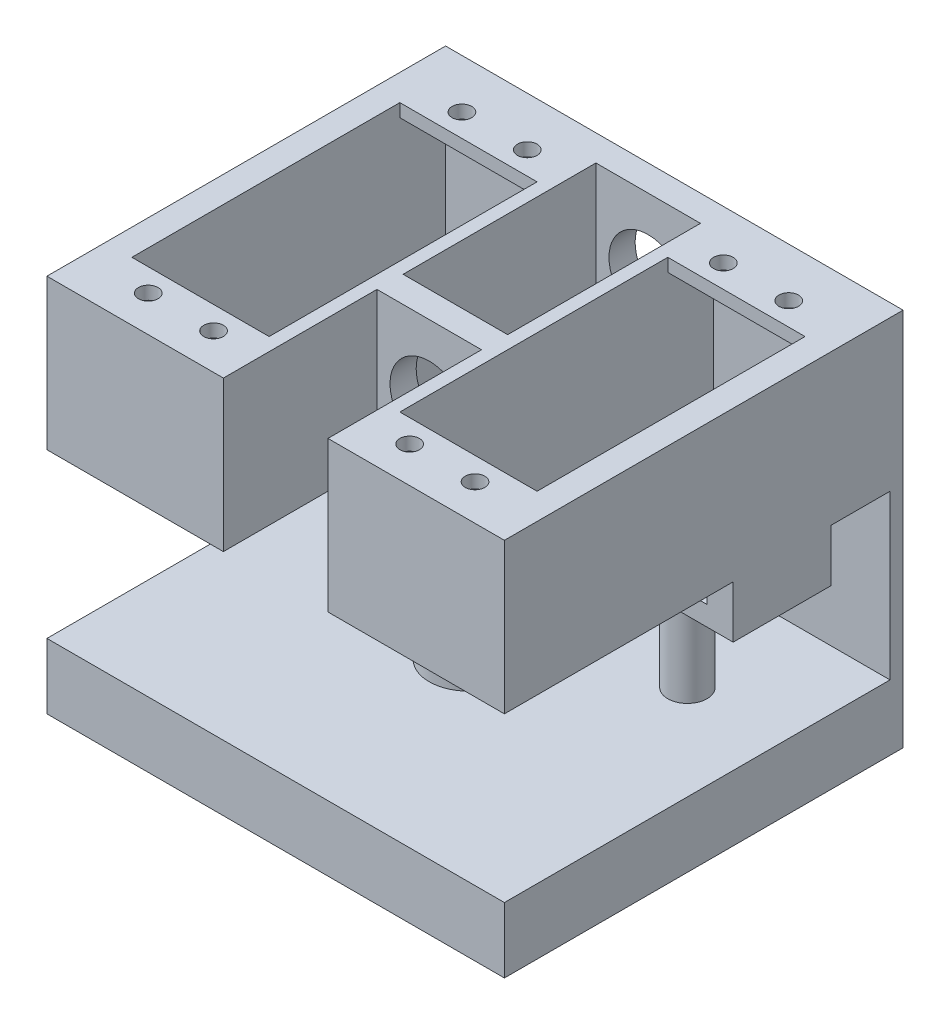
SolidWorks part; units mm, degrees
ref_plane "정면" through (0, 0, 0) normal (0, 0, 1) x (1, 0, 0)
ref_plane "윗면" through (0, 0, 0) normal (0, 1, 0) x (1, 0, 0)
ref_plane "우측면" through (0, 0, 0) normal (1, 0, 0) x (0, 0, -1)
sketch "스케치1" plane through (0, 0, 0) normal (0, 1, 0) x (1, 0, 0)
  line L0 (0, 0) -> (0, 59)
  line L1 (0, 59) -> (-25, 59)
  line L2 (-25, 59) -> (-25, 57)
  line L3 (0, 0) -> (-25, 0)
  line L4 (-45, 0) -> (-45, 2)
  line L5 (-66, 57) -> (-66, 2)
  line L6 (-45, 2) -> (-66, 2)
  line L7 (-45, 59) -> (-70, 59)
  line L8 (-70, 59) -> (-70, 0)
  line L9 (-70, 0) -> (-45, 0)
  line L10 (0, 0) -> (-4, 0)
  line L11 (-4, 2) -> (-4, 57)
  line L12 (-4, 57) -> (-25, 57)
  line L13 (-70, 0) -> (-66, 0)
  line L15 (-66, 57) -> (-45, 57)
  line L16 (-45, 57) -> (-45, 59)
  line L17 (-25, 0) -> (-25, 2)
  line L18 (-25, 2) -> (-4, 2)
extrude "보스-돌출1" add sketch "스케치1" along normal blind 23 contours L15 L16 L7 L8 L9 L4 L6 L5 | L18 L17 L3 L0 L1 L2 L12 L11
sketch "스케치2" plane through (0, 23, 0) normal (0, 1, 0) x (1, 0, 0)
  line L0 (-45, 59) -> (-45, 50)
  line L1 (-45, 50) -> (-66, 50)
  line L2 (-66, 57) -> (-66, 2) construction
  line L3 (-66, 50) -> (-66, 59)
  line L4 (-45, 59) -> (-70, 59) construction
  line L5 (-66, 59) -> (-45, 59)
  line L6 (-25, 59) -> (-25, 50)
  line L7 (-25, 50) -> (-4, 50)
  line L8 (-4, 2) -> (-4, 57) construction
  line L9 (-4, 50) -> (-4, 59)
  line L10 (0, 59) -> (-25, 59) construction
  line L11 (-4, 59) -> (-25, 59)
  line L12 (-45, 0) -> (-45, 9)
  line L13 (-45, 9) -> (-66, 9)
  line L14 (-66, 9) -> (-66, 0)
  line L15 (-70, 0) -> (-45, 0) construction
  line L16 (-66, 0) -> (-45, 0)
  line L17 (-25, 0) -> (-4, 0)
  line L18 (0, 0) -> (-25, 0) construction
  line L19 (-4, 0) -> (-4, 9)
  line L20 (-4, 9) -> (-25, 9)
  line L21 (-25, 9) -> (-25, 0)
extrude "보스-돌출2" add sketch "스케치2" against normal blind 2
sketch "스케치3" plane through (0, 23, 0) normal (0, 1, 0) x (1, 0, 0)
  circle A0 centre (-50, 53.5) radius 1.5
  circle A1 centre (-60, 53.5) radius 1.5
  circle A2 centre (-20, 53.5) radius 1.5
  circle A3 centre (-10, 53.5) radius 1.5
  circle A4 centre (-60, 5.5) radius 1.5
  circle A5 centre (-50, 5.5) radius 1.5
  circle A6 centre (-20, 5.5) radius 1.5
  circle A7 centre (-10, 5.5) radius 1.5
extrude "컷-돌출1" cut sketch "스케치3" against normal blind 2
sketch "스케치4" plane through (-25, 0, 0) normal (-1, 0, 0) x (0, 0, 1)
  line L0 (-59, 23) -> (-54.5, 23)
  line L1 (-59, 23) -> (-50, 23) construction
  line L2 (-54.5, 23) -> (-54.5, 0)
  line L3 (-54.5, 0) -> (-59, 0)
  line L4 (-59, 0) -> (-59, 23)
extrude "보스-돌출3" add sketch "스케치4" along normal blind 20
sketch "스케치5" plane through (0, 0, -54.5) normal (0, 0, 1) x (1, 0, 0)
  line L1 (-25, 0) -> (-45, 0)
  line L2 (-25, 0) -> (-25, 23)
  line L3 (-25, 23) -> (-45, 23)
  line L4 (-45, 0) -> (-45, 23)
extrude "보스-돌출4" add sketch "스케치5" along normal blind 54.5
sketch "스케치7" plane through (0, 0, 0) normal (0, -1, 0) x (1, 0, 0)
  circle A0 centre (-35, -29.5) radius 6
extrude "보스-돌출5" add sketch "스케치7" along normal blind 35
sketch "스케치8" plane through (0, 0, 0) normal (0, -1, 0) x (1, 0, 0)
  line L0 (-4, -50) -> (0, -50)
  line L1 (0, 0) -> (0, -59) construction
  line L2 (0, -50) -> (0, -35)
  line L3 (0, -35) -> (-4, -35)
  line L5 (-4, -2) -> (-4, -57) construction
  line L6 (-4, -35) -> (-4, -50)
  line L7 (-66, -50) -> (-66, -35)
  line L8 (-66, -57) -> (-66, -2) construction
  line L9 (-66, -35) -> (-70, -35)
  line L10 (-70, -59) -> (-70, 0) construction
  line L11 (-70, -35) -> (-70, -50)
  line L12 (-70, -50) -> (-66, -50)
extrude "보스-돌출6" add sketch "스케치8" along normal blind 5
sketch "스케치9" plane through (0, -5, 0) normal (0, -1, 0) x (1, 0, 0)
  line L0 (-70, -50) -> (-45, -50)
  line L1 (-45, -50) -> (0, -50)
  line L2 (0, -50) -> (0, -35)
  line L3 (0, -35) -> (-70, -35)
  line L4 (-70, -35) -> (-70, -50)
extrude "보스-돌출7" add sketch "스케치9" along normal blind 3
sketch "스케치10" plane through (0, 0, 0) normal (0, -1, 0) x (1, 0, 0)
  circle A0 centre (-35, -42.5) radius 5
extrude "보스-돌출8" add sketch "스케치10" along normal blind 35
sketch "스케치11" plane through (0, -35, 0) normal (0, -1, 0) x (1, 0, 0)
  line L2 (-35, -29.5) -> (-33, -29.5)
  line L3 (-33, -29.5) -> (-33, -42.5)
  line L4 (-33, -42.5) -> (-37, -42.5)
  line L5 (-37, -42.5) -> (-37, -29.5)
  line L6 (-37, -29.5) -> (-35, -29.5)
extrude "보스-돌출9" add sketch "스케치11" against normal blind 35
sketch "스케치12" plane through (0, -8, 0) normal (0, -1, 0) x (1, 0, 0)
  circle A0 centre (-55.5, -42.5) radius 3
  circle A1 centre (-14.5, -42.5) radius 3
extrude "보스-돌출10" add sketch "스케치12" along normal blind 27
sketch "스케치13" plane through (0, 0, 0) normal (0, -1, 0) x (1, 0, 0)
  line L3 (-35, -23.5) -> (-27, -23.5)
  line L4 (-27, -23.5) -> (-27, -2)
  line L5 (-27, -2) -> (-43, -2)
  line L6 (-43, -2) -> (-43, -23.5)
  line L7 (-43, -23.5) -> (-35, -23.5)
  arc A0 (-33, -35.1569) -> (-37, -35.1569) centre (-35, -29.5) ccw construction
extrude "컷-돌출2" cut sketch "스케치13" against normal blind 27
sketch "스케치14" plane through (0, 23, 0) normal (0, 1, 0) x (1, 0, 0)
  line L5 (-35, 57) -> (-43, 57)
  line L6 (-43, 57) -> (-27, 57)
  line L9 (-35, 27.5) -> (-43, 27.5)
  line L10 (-43, 27.5) -> (-27, 27.5)
  line L11 (-27, 27.5) -> (-27, 57)
  line L12 (-43, 57) -> (-43, 27.5)
  line L13 (-43, 27.5) -> (-42.7303, 27.3871)
extrude "컷-돌출3" cut sketch "스케치14" against normal blind 20 contours L5 L12 L9 L10 L11 L6
sketch "스케치15" plane through (0, 0, -59) normal (0, 0, -1) x (-1, 0, 0)
  line L0 (0, 0) -> (0, 23)
  line L2 (0, 23) -> (70, 23)
  line L3 (0, 0) -> (0, -35)
  line L4 (0, -35) -> (70, -35)
  line L5 (70, -35) -> (70, 23)
extrude "보스-돌출11" add sketch "스케치15" along normal blind 2
sketch "스케치16" plane through (0, 0, -59) normal (0, 0, 1) x (1, 0, 0)
  line L0 (-52.5, -35) -> (-52.5, -8)
  line L1 (-52.5, -8) -> (-17.5, -8)
  line L2 (-17.5, -8) -> (-17.5, -35)
  line L3 (-17.5, -35) -> (-52.5, -35)
extrude "컷-돌출5" cut sketch "스케치16" against normal blind 2
sketch "스케치18" plane through (0, 23, 0) normal (0, 1, 0) x (1, 0, 0)
  line L0 (-43, 2) -> (-43, 0)
  line L1 (-70, 0) -> (0, 0) construction
  line L2 (-43, 0) -> (-27, 0)
  line L3 (-27, 0) -> (-27, 2)
  line L4 (-27, 2) -> (-43, 2)
extrude "컷-돌출7" cut sketch "스케치18" against normal blind 30
sketch "스케치19" plane through (0, 0, -23.5) normal (0, 0, 1) x (1, 0, 0)
  circle A0 centre (-35, 11.5) radius 3
extrude "컷-돌출8" cut sketch "스케치19" against normal blind 50
sketch "스케치20" plane through (0, -35, 0) normal (0, -1, 0) x (1, 0, 0)
  line L1 (-35, 0) -> (0, 0)
  line L2 (0, 0) -> (0, -61)
  line L3 (0, -61) -> (-70, -61)
  line L4 (-70, -61) -> (-70, 0)
  line L5 (-70, 0) -> (-35, 0)
extrude "보스-돌출12" add sketch "스케치20" against normal blind 10
sketch "스케치21" plane through (0, 0, -23.5) normal (0, 0, 1) x (1, 0, 0)
  circle A0 centre (-35, 11.5) radius 6
extrude "컷-돌출9" cut sketch "스케치21" against normal blind 60
